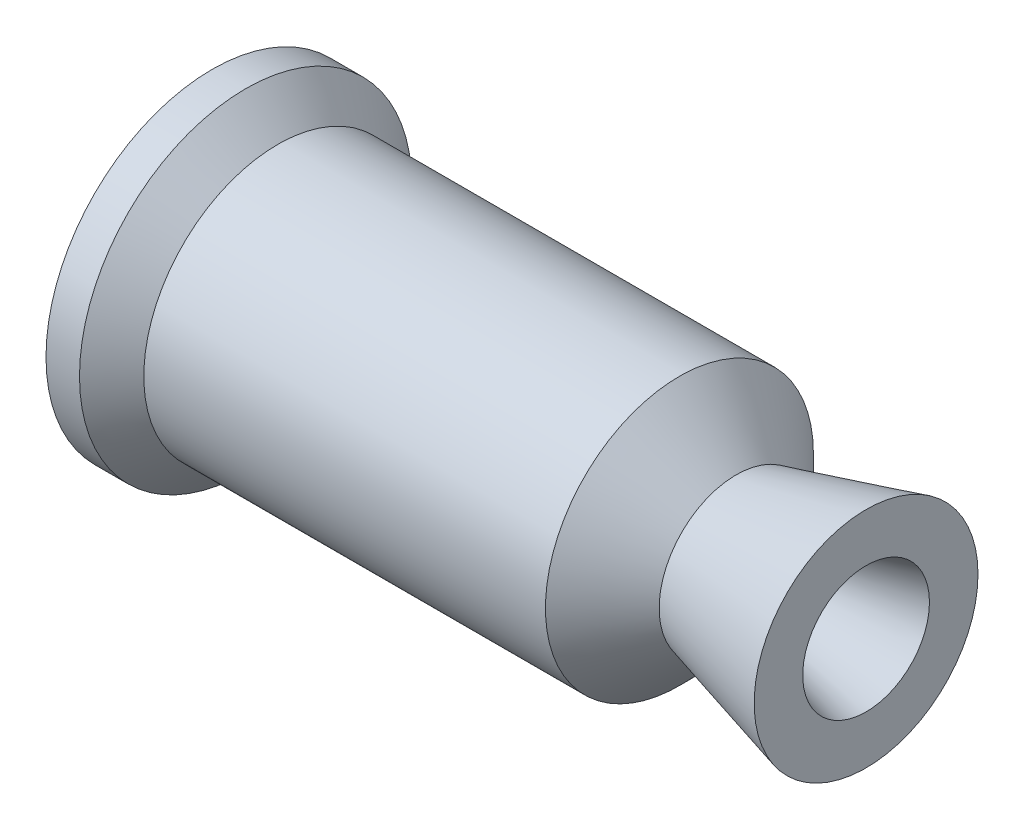
SolidWorks part; units mm, degrees
other "Markup1"
sketch "Sketch3" plane through (0, 31.496, 31.496) normal (-0.2495, 0.0339, 0.9678) x (0.2498, 0.9678, 0.0305)
material "Cast Carbon Steel"
ref_plane "Front Plane" through (0, 0, 0) normal (0, 0, 1) x (1, 0, 0)
ref_plane "Top Plane" through (0, 0, 0) normal (0, 1, 0) x (1, 0, 0)
ref_plane "Right Plane" through (0, 0, 0) normal (1, 0, 0) x (0, 0, -1)
sketch "Sketch1" plane through (0, 0, 0) normal (0, 0, 1) x (1, 0, 0)
  line L0 (0, 0) -> (0, 18.8722) construction
  line L1 (0, 18.8722) -> (82.55, 18.8722)
  line L2 (82.55, 18.8722) -> (95.4532, 5.969)
  line L3 (95.4532, 5.969) -> (101.4222, 5.969)
  line L4 (101.4222, 5.969) -> (123.9832, 12.0142)
  line L5 (123.9832, 12.0142) -> (123.9832, 25.4)
  line L6 (123.9832, 25.4) -> (0, 25.4)
  line L7 (0, 25.4) -> (0, 18.8722)
  line L8 (88.5946, 25.4) -> (99.3715, 14.6231)
  line L10 (99.3715, 14.6231) -> (123.9832, 21.2178)
  line L11 (22.3107, 25.4) -> (22.3107, 18.8722) construction
  line L12 (91.1758, 22.8188) -> (84.8896, 16.5326) construction
  line L13 (112.1383, 18.044) -> (114.4392, 9.4569) construction
  line L14 (0, 0) -> (-20.4849, 0) construction
  line L15 (6.35, 31.496) -> (12.446, 25.4)
  line L16 (0, 25.4) -> (0, 31.496)
  line L17 (0, 31.496) -> (6.35, 31.496)
  line L18 (6.35, 31.496) -> (6.35, 25.4)
  dimension "D1" = 18.8722
  dimension "D2" = 25.4
  dimension "D3" = 5.969
  dimension "D4" = 135
  dimension "D5" = 165
  dimension "D6" = 5.969
  dimension "D7" = 12.0142
  dimension "D8" = 82.55
  dimension "D9" = 6.096
  dimension "D10" = 135
  dimension "D11" = 6.35
  dimension "D13" = 8.89
revolve "Revolve1" add sketch "Sketch1" angle 360 about L14
fillet "Fillet8" [suppressed] radius 12.7
fillet "Fillet9" [suppressed] radius 3.81
sketch "Sketch2" plane through (0, 0, 0) normal (-1, 0, 0) x (0, 0, 1)
  line L0 (0, 0) -> (0, 22.0599)
  line L1 (0, 22.0599) -> (0, 23.368) construction
  line L2 (0, 23.368) -> (0, 24.6761) construction
  line L3 (0, 24.6761) -> (0, 26.8224) construction
  line L4 (0, 26.8224) -> (0, 28.1305) construction
  line L5 (0, 28.1305) -> (0, 29.4386) construction
  circle A0 centre (0, 0) radius 26.8224 construction
  circle A1 centre (0, 0) radius 29.4386 construction
  circle A2 centre (0, 0) radius 24.6761 construction
  circle A3 centre (0, 0) radius 22.0599 construction
  circle A4 centre (0, 0) radius 23.368 construction
  circle A5 centre (0, 0) radius 28.1305 construction
  circle A6 centre (0, 0) radius 24.9555
  circle A7 centre (0, 0) radius 21.7805
  circle A8 centre (0, 0) radius 29.718
  circle A9 centre (0, 0) radius 26.543
  dimension "D1" = 58.8772
  dimension "D2" = 53.6448
  dimension "D3" = 49.3522
  dimension "D4" = 44.1198
  dimension "D5" = 1.5875
  dimension "D6" = 1.5875
  dimension "D7" = 1.5875
  dimension "D8" = 1.5875
extrude "Cut-Extrude1" cut sketch "Sketch2" against normal blind 2.032 contours A2 A3 | A1 A0 | A8 A9 | A6
